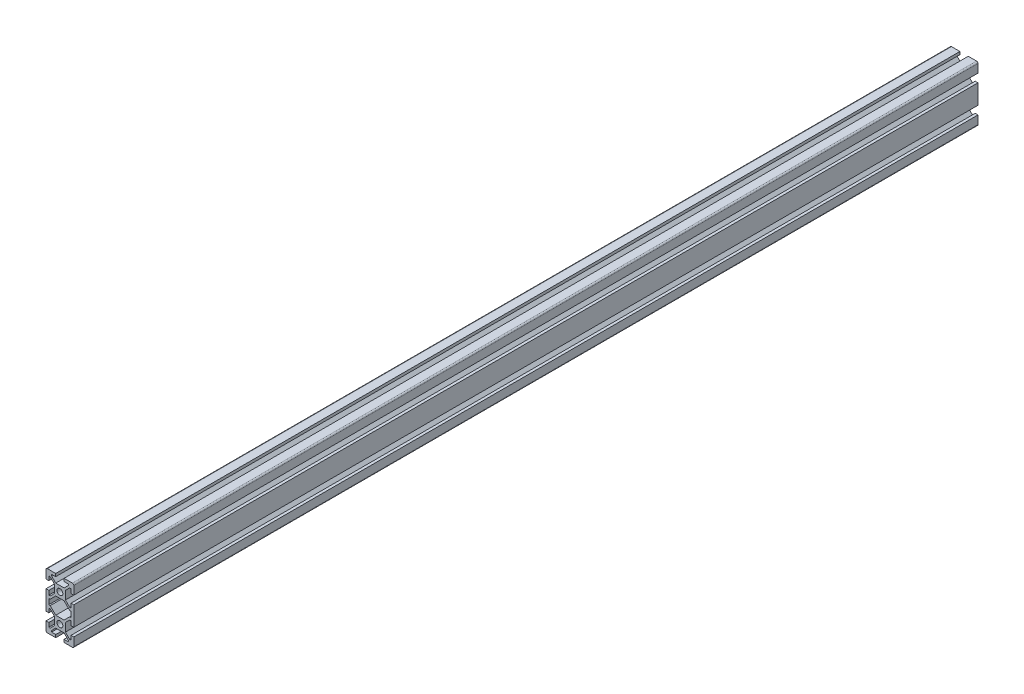
SolidWorks part; units mm, degrees
material "6063-O, Barra estrusa (SS)"
ref_plane "Piano frontale" through (0, 0, 0) normal (0, 0, 1) x (1, 0, 0)
ref_plane "Piano superiore" through (0, 0, 0) normal (0, 1, 0) x (1, 0, 0)
ref_plane "Piano destro" through (0, 0, 0) normal (1, 0, 0) x (0, 0, -1)
other "Lunghezza"
other "Lunghezze"
sketch "Schizzo1" plane through (0, 0, 0) normal (0, 0, 1) x (1, 0, 0)
  line L0 (-6, 18) -> (6, 18) construction
  line L1 (10, 20) -> (-10, 20) construction
  line L2 (10, 20) -> (10, -20) construction
  line L3 (-8, 4) -> (-8, -4) construction
  line L4 (-10, 20) -> (-10, -20) construction
  line L5 (10, 20) -> (-10, 0) construction
  line L6 (10, 0) -> (-10, 20) construction
  line L7 (-3, 14) -> (3, 14) construction
  line L8 (-3, 32.3825) -> (-3, 22.2883) construction
  line L9 (0, 33.8953) -> (0, -6.3729) construction
  line L10 (3, 32.3825) -> (3, 22.2883) construction
  line L11 (-6, 11.8152) -> (-6, 23.4013) construction
  line L12 (6, 10.4596) -> (6, 33.4013) construction
  line L13 (-3, 14) -> (-9, 20) construction
  line L14 (-10, 20) -> (-3, 20)
  line L15 (-3, 20) -> (-3, 18)
  line L16 (-3, 18) -> (-6, 18)
  line L17 (-6, 18) -> (-6, 17)
  line L18 (-6, 17) -> (-3, 14)
  line L19 (-3, 14) -> (3, 14)
  line L20 (3, 14) -> (9, 20) construction
  line L21 (3, 14) -> (6, 17)
  line L22 (6, 17) -> (6, 18)
  line L23 (6, 18) -> (3, 18)
  line L24 (3, 18) -> (3, 20)
  line L25 (3, 20) -> (10, 20)
  line L26 (10, 20) -> (10, 13)
  line L27 (10, 13) -> (8, 13)
  line L28 (8, 13) -> (8, 16)
  line L29 (8, 16) -> (7, 16)
  line L30 (7, 16) -> (4, 13)
  line L31 (4, 13) -> (4, 7)
  line L32 (4, 7) -> (7, 4)
  line L33 (8, 4) -> (8, 7)
  line L34 (7, 4) -> (8, 4)
  line L35 (8, 7) -> (10, 7)
  line L36 (10, 7) -> (10, 0)
  line L37 (8, 4) -> (8, -4) construction
  line L38 (-7, 4) -> (-7, -4) construction
  line L39 (7, 4) -> (7, -4) construction
  line L40 (3, -6) -> (7, -2)
  line L41 (-3, 6) -> (-7, 2)
  line L42 (3, 6) -> (-3, 6)
  line L43 (3, 6) -> (7, 2)
  line L44 (-3, -6) -> (-7, -2)
  line L45 (-7, -2) -> (-8, -2)
  line L46 (-8, -2) -> (-8, 2)
  line L47 (-8, 2) -> (-7, 2)
  line L48 (-10, 0) -> (-10, 7)
  line L49 (-10, 7) -> (-8, 7)
  line L50 (-8, 7) -> (-8, 4)
  line L51 (-8, 4) -> (-7, 4)
  line L52 (-7, 4) -> (-4, 7)
  line L53 (-4, 7) -> (-4, 13)
  line L54 (-4, 13) -> (-7, 16)
  line L55 (-8, 16) -> (-8, 13)
  line L56 (-7, 16) -> (-8, 16)
  line L57 (-8, 13) -> (-10, 13)
  line L58 (-10, 13) -> (-10, 20)
  line L59 (-19.9461, 0) -> (34.5024, 0) construction
  line L60 (3, -14) -> (9, -20) construction
  line L61 (-3, -14) -> (-9, -20) construction
  line L62 (-3, -14) -> (3, -14) construction
  line L63 (10, 0) -> (-10, -20) construction
  line L64 (10, -20) -> (-10, 0) construction
  line L65 (10, -20) -> (-10, -20) construction
  line L66 (-6, -18) -> (6, -18) construction
  line L67 (-10, -13) -> (-10, -20)
  line L68 (-8, -13) -> (-10, -13)
  line L69 (-7, -16) -> (-8, -16)
  line L70 (-8, -16) -> (-8, -13)
  line L71 (-4, -13) -> (-7, -16)
  line L72 (-4, -7) -> (-4, -13)
  line L73 (-7, -4) -> (-4, -7)
  line L74 (-8, -4) -> (-7, -4)
  line L75 (-8, -7) -> (-8, -4)
  line L76 (-10, -7) -> (-8, -7)
  line L77 (-10, 0) -> (-10, -7)
  line L78 (7, -2) -> (8, -2)
  line L79 (8, -2) -> (8, 2)
  line L80 (8, 2) -> (7, 2)
  line L81 (3, -6) -> (-3, -6)
  line L85 (10, -7) -> (10, 0)
  line L86 (8, -7) -> (10, -7)
  line L87 (7, -4) -> (8, -4)
  line L88 (8, -4) -> (8, -7)
  line L89 (4, -7) -> (7, -4)
  line L90 (4, -13) -> (4, -7)
  line L91 (7, -16) -> (4, -13)
  line L92 (8, -16) -> (7, -16)
  line L93 (8, -13) -> (8, -16)
  line L94 (10, -13) -> (8, -13)
  line L95 (10, -20) -> (10, -13)
  line L96 (3, -20) -> (10, -20)
  line L97 (3, -18) -> (3, -20)
  line L98 (6, -18) -> (3, -18)
  line L99 (6, -17) -> (6, -18)
  line L100 (3, -14) -> (6, -17)
  line L101 (-3, -14) -> (3, -14)
  line L102 (-6, -17) -> (-3, -14)
  line L103 (-6, -18) -> (-6, -17)
  line L104 (-3, -18) -> (-6, -18)
  line L105 (-3, -20) -> (-3, -18)
  line L106 (-10, -20) -> (-3, -20)
  line L107 (-3, 0) -> (-10, 0) [skipped]
  line L108 (-3, 0) -> (-3, -2) [skipped]
  line L109 (3, 0) -> (3, 2) [skipped]
  line L110 (10, 0) -> (3, 0) [skipped]
  line L111 (-6, 3) -> (-6, 2) [skipped]
  line L112 (-6, 2) -> (-3, 2) [skipped]
  line L113 (3, 2) -> (6, 2) [skipped]
  line L114 (6, 2) -> (6, 3) [skipped]
  line L115 (-3, 6) -> (-6, 3) [skipped]
  line L116 (6, 3) -> (3, 6) [skipped]
  circle A0 centre (0, 10) radius 2.1
  circle A1 centre (0, -10) radius 2.1
  point P0 (0, 10)
  point P5 (0, 14)
  point P11 (0, 18)
  point P71 (0, 10)
  dimension "D8" = 4.2
  dimension "D14" = 4.2
  dimension "D2" = 20
  dimension "D3" = 2
  dimension "D4" = 4
  dimension "D5" = 6
  dimension "D6" = 12
  dimension "D7" = 4
  dimension "D9" = 6
  dimension "D10" = 3
  dimension "D11" = 20
  dimension "D12" = 40
  dimension "D13" = 20
extrude "Estrusione-Estrusione1" add sketch "Schizzo1" along normal blind 650 contours L67 L106 L105 L104 L103 L102 L101 L100 L99 L98 L97 L96 L95 L94 L93 L92 L91 L90 L89 L87 L88 L86 L85 L36 L35 L33 L34 L32 L31 L30 L29 L28 L27 L26 L25 L24 L23 L22 L21 L19 L18 L17 L16 L15 L14 L58 L57 L55 L56 L54 L53
fillet "Raccordo1" radius 1 4 edges at (-10, -20, 325) (10, -20, 325) (-10, 20, 325) (10, 20, 325)
